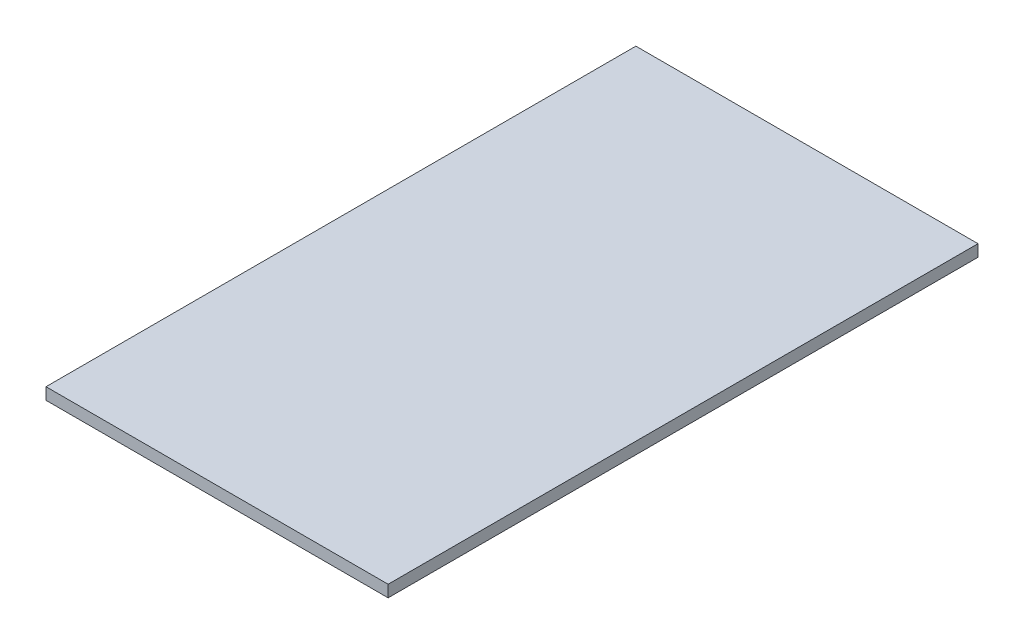
SolidWorks part; units mm, degrees
ref_plane "Front Plane" through (0, 0, 0) normal (0, 0, 1) x (1, 0, 0)
ref_plane "Top Plane" through (0, 0, 0) normal (0, 1, 0) x (1, 0, 0)
ref_plane "Right Plane" through (0, 0, 0) normal (1, 0, 0) x (0, 0, -1)
sketch "Sketch1" plane through (0, 0, 0) normal (0, 1, 0) x (1, 0, 0)
  line L1 (0, 0) -> (184.15, 0)
  line L2 (0, 0) -> (0, 317.5)
  line L3 (0, 317.5) -> (184.15, 317.5)
  line L4 (184.15, 0) -> (184.15, 317.5)
  dimension "D1" = 184.15
  dimension "D2" = 317.5
extrude "Boss-Extrude1" add sketch "Sketch1" along normal blind 6.35
